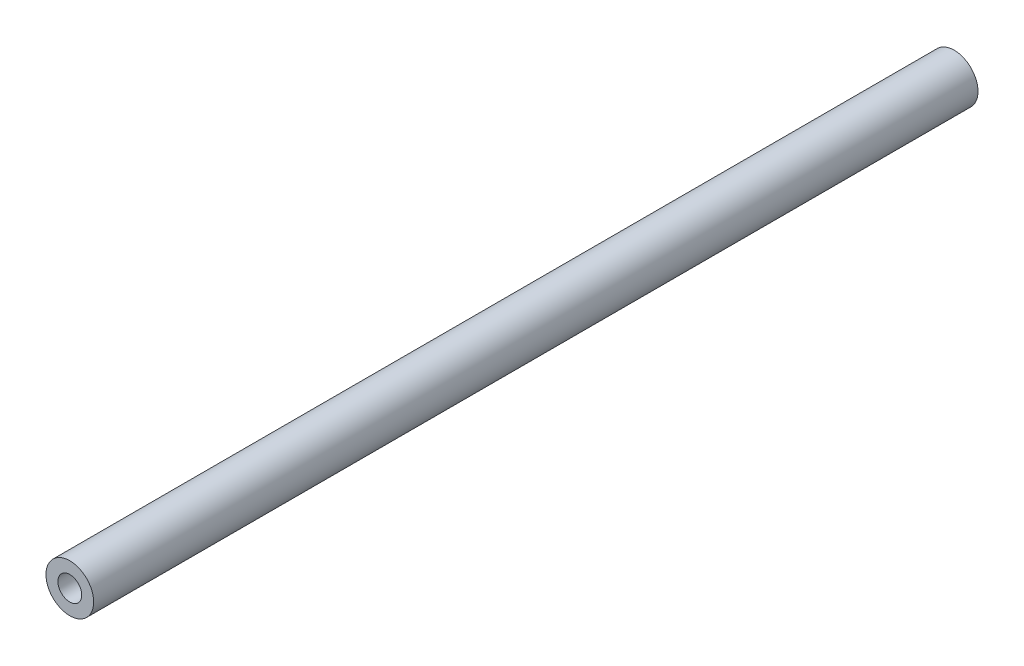
SolidWorks part; units mm, degrees
ref_plane "正面" through (0, 0, 0) normal (0, 0, 1) x (1, 0, 0)
ref_plane "平面" through (0, 0, 0) normal (0, 1, 0) x (1, 0, 0)
ref_plane "右側面" through (0, 0, 0) normal (1, 0, 0) x (0, 0, -1)
sketch "ｽｹｯﾁ1" plane through (0, 0, 0) normal (0, 0, 1) x (1, 0, 0)
  circle A1 centre (0, 0) radius 2.5
  dimension "D1" = 5
extrude "ﾎﾞｽ - 押し出し1" add sketch "ｽｹｯﾁ1" along normal mid plane 92.7
hole_wizard "M3x0.5 ねじ穴1" positions "3Dｽｹｯﾁ1" profile "ｽｹｯﾁ2" tap size "M3x0.5" standard "JIS"
sketch3d "3Dｽｹｯﾁ1"
  line L0 (0, 0, 46.35) -> (0, 0, -46.35) construction
  point P0 (0, 0, 46.35)
  point P4 (0, 0, -46.35)
sketch "ｽｹｯﾁ2" plane through (0, 0, 46.35) normal (1, 0, 0) x (0, -1, 0)
  line L0 (0, 0) -> (0, 9.2511)
  line L1 (0, 9.2511) -> (1.25, 8.5)
  line L2 (1.25, 8.5) -> (1.25, 0)
  line L5 (1.25, 0) -> (0, 0)
  line L10 (0, 9.2511) -> (-1.25, 8.5) construction
  line L11 (0, -6.35) -> (0, 107.95) construction
  dimension "ねじ下穴ﾄﾞﾘﾙ直径" = 2.5
  dimension "ねじ下穴ﾄﾞﾘﾙの深さ" = 8.5
  dimension "ﾄﾞﾘﾙ角度" = 118
cosmetic thread "穴のねじ山1" parameters "D1"=6, "D2"=3
cosmetic thread "穴のねじ山2" parameters "D1"=6, "D2"=3
